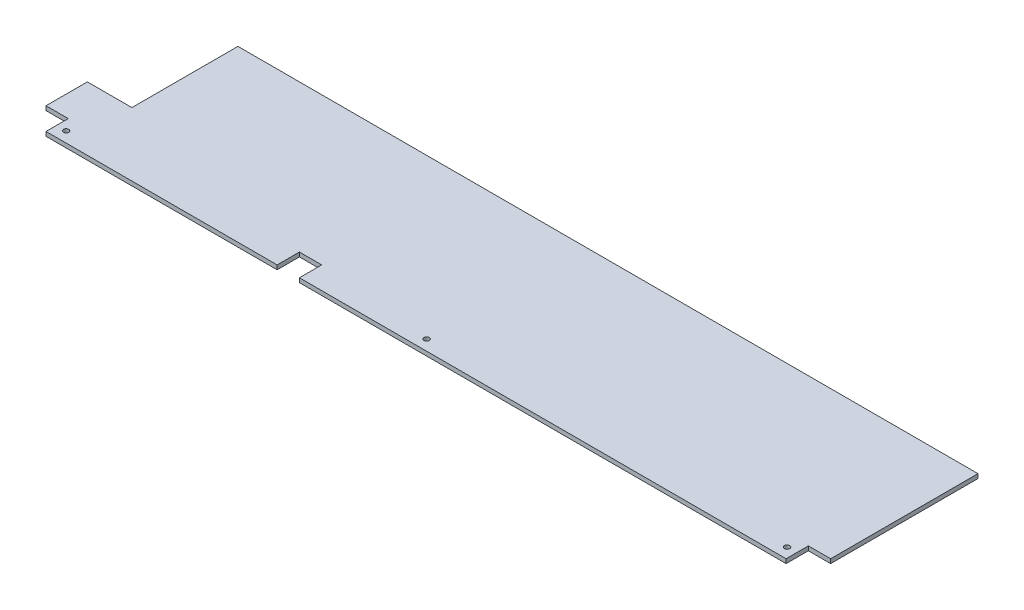
SolidWorks part; units mm, degrees
ref_plane "Front Plane" through (0, 0, 0) normal (0, 0, 1) x (1, 0, 0)
ref_plane "Top Plane" through (0, 0, 0) normal (0, 1, 0) x (1, 0, 0)
ref_plane "Right Plane" through (0, 0, 0) normal (1, 0, 0) x (0, 0, -1)
sketch "Sketch1" plane through (0, 0, 0) normal (0, 1, 0) x (1, 0, 0)
  line L0 (0, 90) -> (0, -90) construction
  line L1 (-370, -90) -> (370, -90) construction
  line L2 (-370, -90) -> (-370, 90) construction
  line L3 (-370, 90) -> (370, 90) construction
  line L4 (370, -90) -> (370, 90) construction
  line L5 (-370, -90) -> (370, 90) construction
  line L6 (-370, 90) -> (370, -90) construction
  line L7 (-370, 0) -> (370, 0) construction
  line L8 (-370, -69) -> (-370, -30)
  line L9 (-370, 90) -> (-328, 90) construction
  line L10 (-370, 90) -> (-370, -30) construction
  line L11 (-370, -30) -> (-328, -30)
  line L12 (-328, 90) -> (-328, -30) construction
  line L13 (-370, -90) -> (-349, -90) construction
  line L14 (-370, -90) -> (-370, -69) construction
  line L15 (-370, -69) -> (-349, -69)
  line L16 (-349, -90) -> (-349, -69)
  line L17 (-328, 90) -> (370, 90) construction
  line L18 (-349, -90) -> (370, -90) construction
  line L19 (-349, -90) -> (-131, -90)
  line L20 (-131, -90) -> (-110, -90) construction
  line L21 (-131, -90) -> (-131, -69)
  line L22 (-131, -69) -> (-110, -69)
  line L23 (-110, -90) -> (-110, -69)
  line L24 (-110, -90) -> (370, -90) construction
  line L25 (-328, 70) -> (370, 70)
  line L26 (-328, 70) -> (-328, -30)
  line L27 (370, 70) -> (370, -90) construction
  line L28 (-110, -90) -> (349, -90)
  line L29 (349, -90) -> (349, -69)
  line L30 (349, -69) -> (370, -69)
  line L31 (370, -69) -> (370, 70)
  circle A0 centre (-340, 80) radius 2.5 construction
  circle A1 centre (0, 80) radius 2.5 construction
  circle A2 centre (340, 80) radius 2.5 construction
  circle A3 centre (-340, -80) radius 2.5
  circle A4 centre (0, -80) radius 2.5
  circle A5 centre (340, -80) radius 2.5
  point P0 (0, 0)
  dimension "D3" = 5
  dimension "D4" = 5
  dimension "D7" = 30
  dimension "D8" = 21
  dimension "D1" = 180
  dimension "D2" = 740
  dimension "D5" = 10
  dimension "D6" = 10
  dimension "D9" = 21
  dimension "D10" = 39
  dimension "D11" = 42
  dimension "D12" = 21
  dimension "D13" = 21
  dimension "D14" = 218
  dimension "D15" = 20
  dimension "D16" = 21
  dimension "D17" = 21
extrude "Boss-Extrude1" add sketch "Sketch1" along normal blind 4
